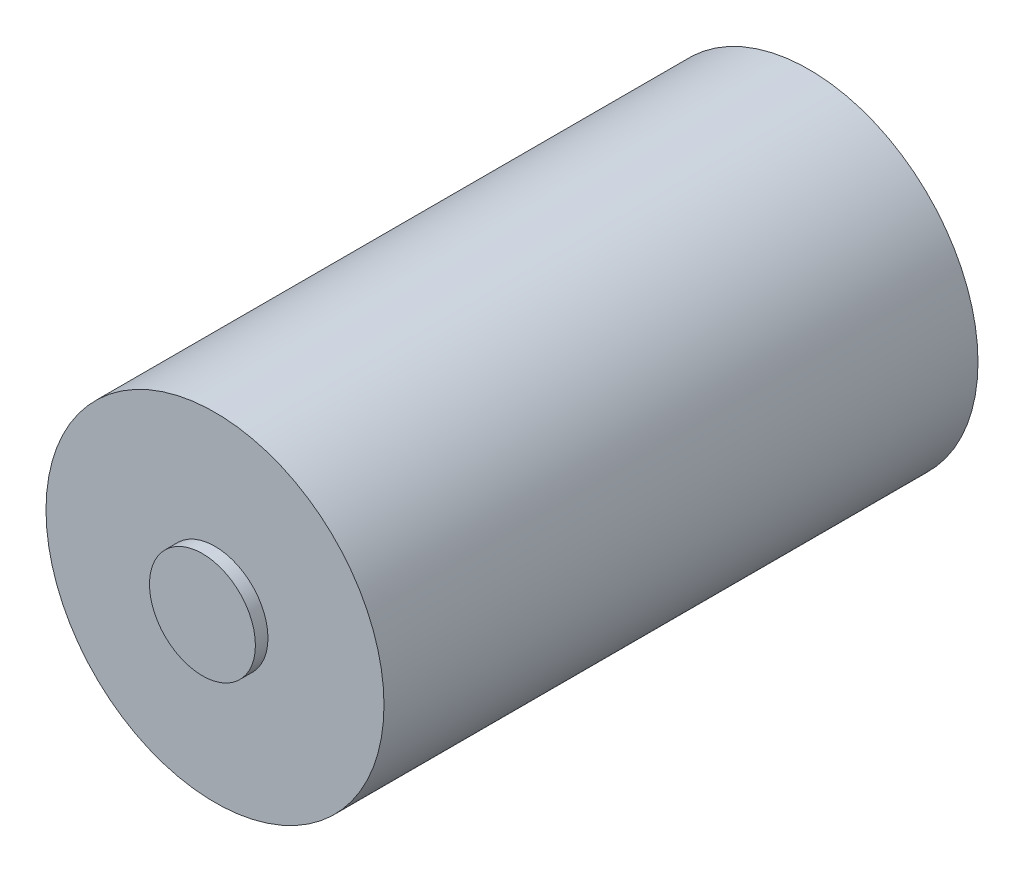
SolidWorks part; units mm, degrees
ref_plane "Front Plane" through (0, 0, 0) normal (0, 0, 1) x (1, 0, 0)
ref_plane "Top Plane" through (0, 0, 0) normal (0, 1, 0) x (1, 0, 0)
ref_plane "Right Plane" through (0, 0, 0) normal (1, 0, 0) x (0, 0, -1)
sketch "Sketch1" plane through (0, 0, 0) normal (0, 0, 1) x (1, 0, 0)
  circle A0 centre (0, 0) radius 6.33
  dimension "D1" = 12.66
extrude "Boss-Extrude1" add sketch "Sketch1" along normal blind 1.5
sketch "Sketch2" plane through (0, 0, 0) normal (0, 0, 1) x (1, 0, 0)
  circle A0 centre (0, 0) radius 20.2
  dimension "D1" = 40.4
extrude "Boss-Extrude2" add sketch "Sketch2" against normal blind 71 contours A0
sketch "Sketch6" plane through (0, 0, -71) normal (0, 0, -1) x (-1, 0, 0)
  circle A1 centre (0, 0) radius 6
  dimension "D2" = 12
extrude "Boss-Extrude4" add sketch "Sketch6" along normal blind 3
sketch "Sketch7" plane through (0, 0, -74) normal (0, 0, -1) x (-1, 0, 0)
  circle A0 centre (0, 0) radius 2
  dimension "D1" = 4
extrude "Boss-Extrude5" add sketch "Sketch7" along normal blind 9
sketch "Sketch8" plane through (0, 0, -71) normal (0, 0, -1) x (-1, 0, 0)
  line L0 (0, 0) -> (-12.5, 0) construction
  line L1 (0, 0) -> (0, -30) construction
  line L2 (0, 0) -> (0, 30) construction
  circle A0 centre (-12.5, 0) radius 1.65
  circle A1 centre (12.5, 0) radius 1.65
  dimension "D2" = 3.3
  dimension "D1" = 12.5
extrude "Cut-Extrude1" cut sketch "Sketch8" against normal blind 4
